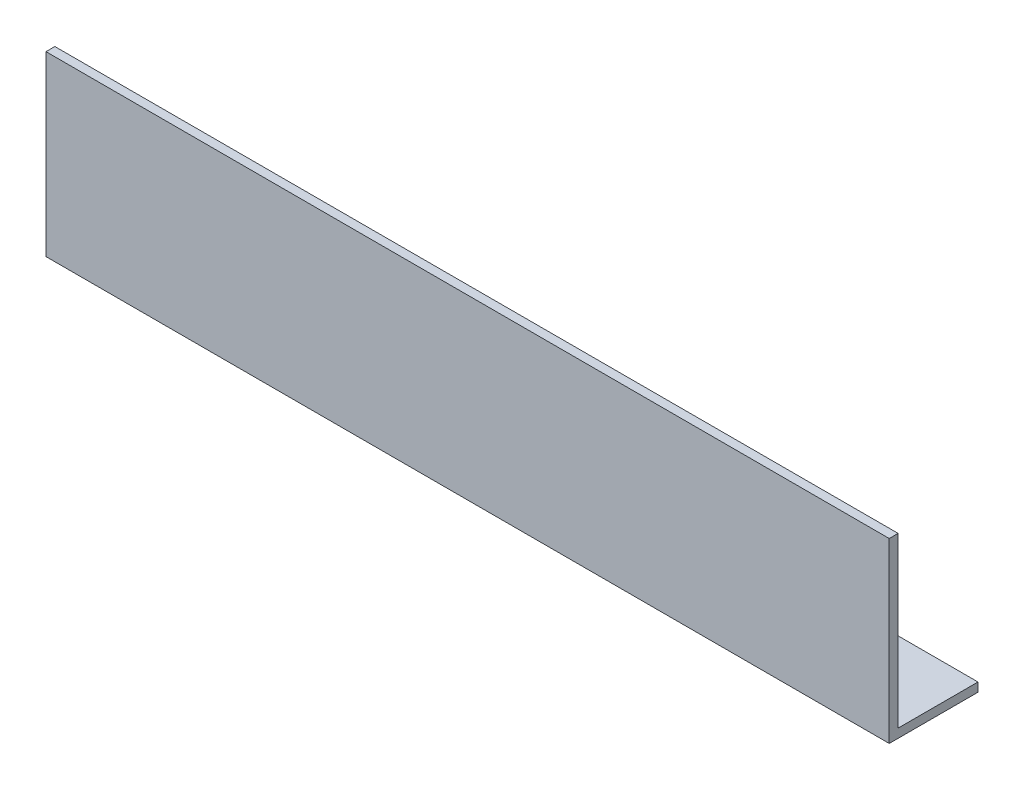
SolidWorks part; units mm, degrees
ref_plane "Спереди" through (0, 0, 0) normal (0, 0, 1) x (1, 0, 0)
ref_plane "Сверху" through (0, 0, 0) normal (0, 1, 0) x (1, 0, 0)
ref_plane "Справа" through (0, 0, 0) normal (1, 0, 0) x (0, 0, -1)
sketch "Эскиз1" plane through (0, 0, 0) normal (1, 0, 0) x (0, 0, -1)
  line L0 (0, 40) -> (0, 0)
  line L1 (0, 0) -> (20, 0)
extrude "Вытянуть-Тонкостенный1" add sketch "Эскиз1" along normal blind 190 thin thin type one direction reverse wall 2
